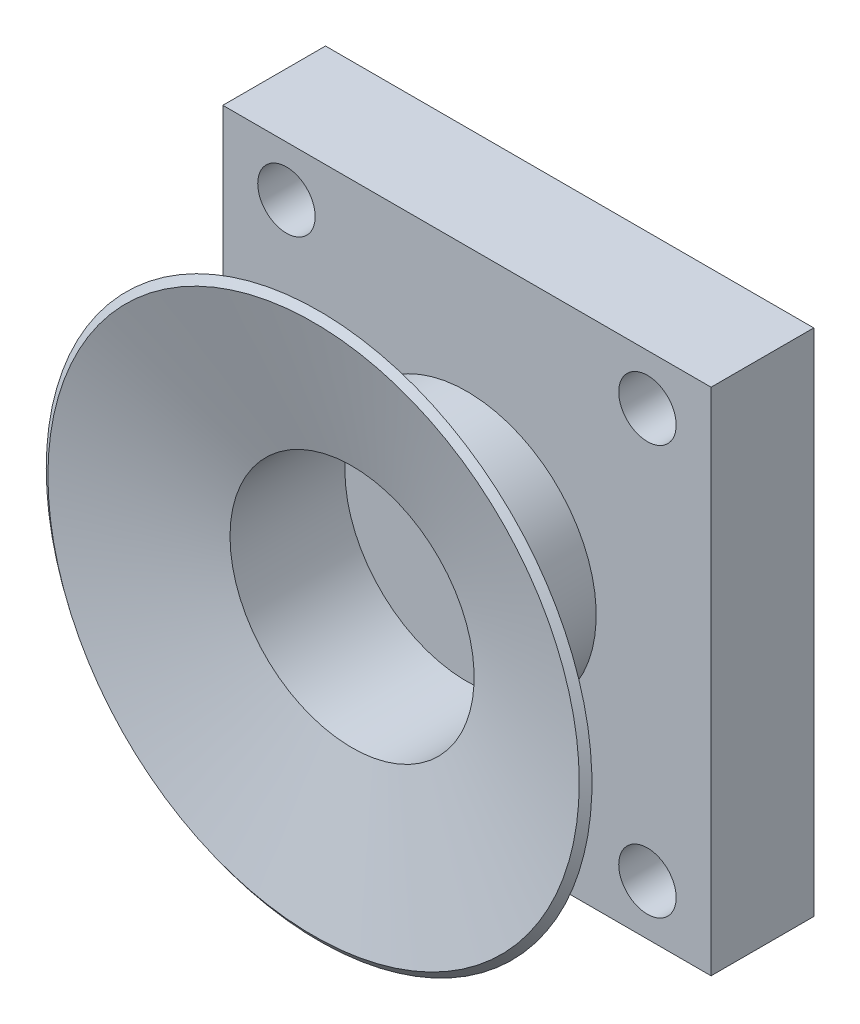
SolidWorks part; units mm, degrees
ref_plane "Front Plane" through (0, 0, 0) normal (0, 0, 1) x (1, 0, 0)
ref_plane "Top Plane" through (0, 0, 0) normal (0, 1, 0) x (1, 0, 0)
ref_plane "Right Plane" through (0, 0, 0) normal (1, 0, 0) x (0, 0, -1)
sketch "Sketch1" plane through (0, 0, 0) normal (0, 0, 1) x (1, 0, 0)
  line L0 (0, 0) -> (0, 35.5)
  line L1 (0, 35.5) -> (34, 35.5)
  line L2 (34, 35.5) -> (34, 0)
  line L3 (34, 0) -> (0, 0)
  line L4 (17, 35.5) -> (17, 0) construction
  line L5 (34, 17.75) -> (0, 17.75) construction
  circle A0 centre (4.4315, 3.5) radius 2
  circle A1 centre (29.5685, 3.5) radius 2
  circle A2 centre (29.5685, 32) radius 2
  circle A3 centre (4.4315, 32) radius 2
  dimension "D4" = 4
  dimension "D1" = 35.5
  dimension "D2" = 34
  dimension "D3" = 3.5
extrude "Boss-Extrude1" add sketch "Sketch1" along normal blind 7.15
sketch "Sketch3" plane through (0, 0, 7.15) normal (0, 0, 1) x (1, 0, 0)
  line L0 (17, 35.5) -> (17, 0) construction
  circle A0 centre (17, 17.75) radius 8.5
  point P4 (17, 17.75)
  dimension "D1" = 17
ref_axis "Axis1" through (17, 17.75, 7.15) along (0, 0, 1)
ref_plane "Plane1" through (17, 0, 0) normal (1, 0, 0) x (0, 0, -1)
sketch "Sketch4" plane through (17, 0, 0) normal (1, 0, 0) x (0, 0, -1)
  line L1 (-7.15, 26.25) -> (-15.15, 26.25)
  line L2 (-15.15, 26.25) -> (-17.8295, 36.25)
  line L4 (-7.15, 17.75) -> (-23.3713, 17.75) construction
  line L5 (-17.8295, 17.75) -> (-7.15, 17.75)
  line L6 (-7.15, 26.75) -> (-14.7663, 26.75)
  line L7 (-14.7663, 26.75) -> (-17.4458, 36.75)
  line L10 (-7.15, 17.25) -> (-7.15, 17.75)
  line L11 (-7.15, 26.25) -> (-7.15, 26.75)
  line L12 (-17.8295, 17.75) -> (-18.3295, 17.75)
  line L14 (-15.15, 26.25) -> (-14.7663, 26.75) construction
  line L15 (-17.4458, 36.75) -> (-17.8295, 36.25)
  point P12 (0, 0)
  dimension "D1" = 8
  dimension "D2" = 105
  dimension "D3" = 10
  dimension "D4" = 8.5
  dimension "D5" = 0.5
  dimension "D6" = 0.5
revolve "Revolve2" add sketch "Sketch4" angle 360 about axis through (17, 17.75, 7.15) along (0, 0, 1)
